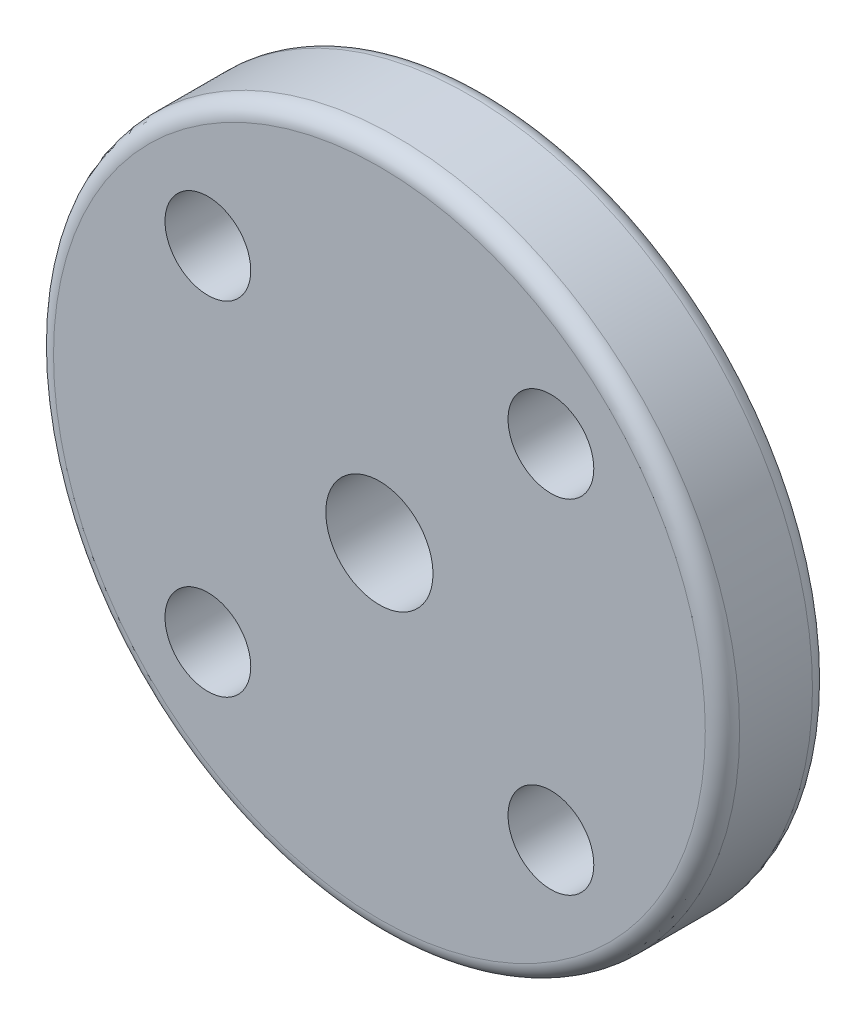
SolidWorks part; units mm, degrees
ref_plane "Front Plane" through (0, 0, 0) normal (0, 0, 1) x (1, 0, 0)
ref_plane "Top Plane" through (0, 0, 0) normal (0, 1, 0) x (1, 0, 0)
ref_plane "Right Plane" through (0, 0, 0) normal (1, 0, 0) x (0, 0, -1)
sketch "Sketch1" plane through (0, 0, 0) normal (0, 0, 1) x (1, 0, 0)
  line L1 (-8, 8) -> (8, 8)
  line L2 (-8, 8) -> (-8, -8)
  line L3 (-8, -8) -> (8, -8)
  line L4 (8, 8) -> (8, -8)
  line L5 (-8, 8) -> (8, -8) construction
  line L6 (-8, -8) -> (8, 8) construction
  circle A0 centre (0, 0) radius 16
  circle A1 centre (-8, 8) radius 2
  circle A2 centre (-8, -8) radius 2
  circle A3 centre (8, -8) radius 2
  circle A4 centre (8, 8) radius 2
  circle A5 centre (0, 0) radius 2.5
  dimension "D1" = 32
  dimension "D4" = 4
  dimension "D5" = 5
  dimension "D2" = 16
  dimension "D3" = 16
extrude "Extrude2" add sketch "Sketch1" along normal blind 5 contours A0 A4 L4 A3 L3 A2 L2 A1 L1 | A4 L1 A1 L2 A2 L3 A3 L4 A5
fillet "Fillet1" radius 0.8 2 edges at (16, 0, 0) (16, 0, 5)
